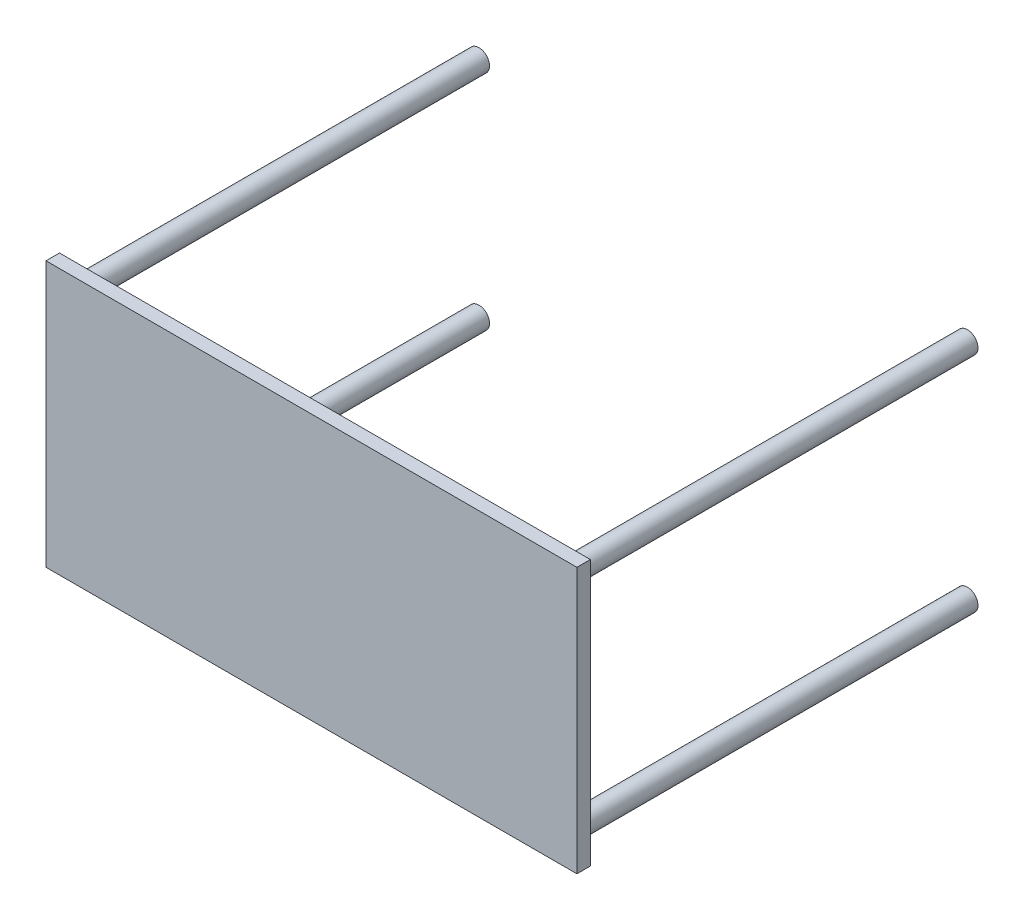
SolidWorks part; units mm, degrees
ref_plane "Front Plane" through (0, 0, 0) normal (0, 0, 1) x (1, 0, 0)
ref_plane "Top Plane" through (0, 0, 0) normal (0, 1, 0) x (1, 0, 0)
ref_plane "Right Plane" through (0, 0, 0) normal (1, 0, 0) x (0, 0, -1)
sketch "Sketch1" plane through (0, 0, 0) normal (0, 0, 1) x (1, 0, 0)
  line L1 (-500, -250) -> (500, -250)
  line L2 (-500, -250) -> (-500, 250)
  line L3 (-500, 250) -> (500, 250)
  line L4 (500, -250) -> (500, 250)
  line L5 (-500, -250) -> (500, 250) construction
  line L6 (-500, 250) -> (500, -250) construction
  point P0 (0, 0)
  dimension "D1" = 500
  dimension "D2" = 1000
extrude "Boss-Extrude1" add sketch "Sketch1" along normal blind 25.4
sketch "Sketch2" plane through (0, 0, 0) normal (0, 0, 1) x (1, 0, 0)
  line L0 (0, 361.9016) -> (0, -387.5675) construction
  line L1 (-573.8503, 0) -> (561.607, 0) construction
  circle A0 centre (460, 210) radius 20
  circle A1 centre (460, -210) radius 20
  circle A2 centre (-460, -210) radius 20
  circle A3 centre (-460, 210) radius 20
  point P9 (0, 85.7803)
  dimension "D2" = 40
  dimension "D1" = 210
  dimension "D3" = 460
extrude "Boss-Extrude2" add sketch "Sketch2" against normal blind 750
